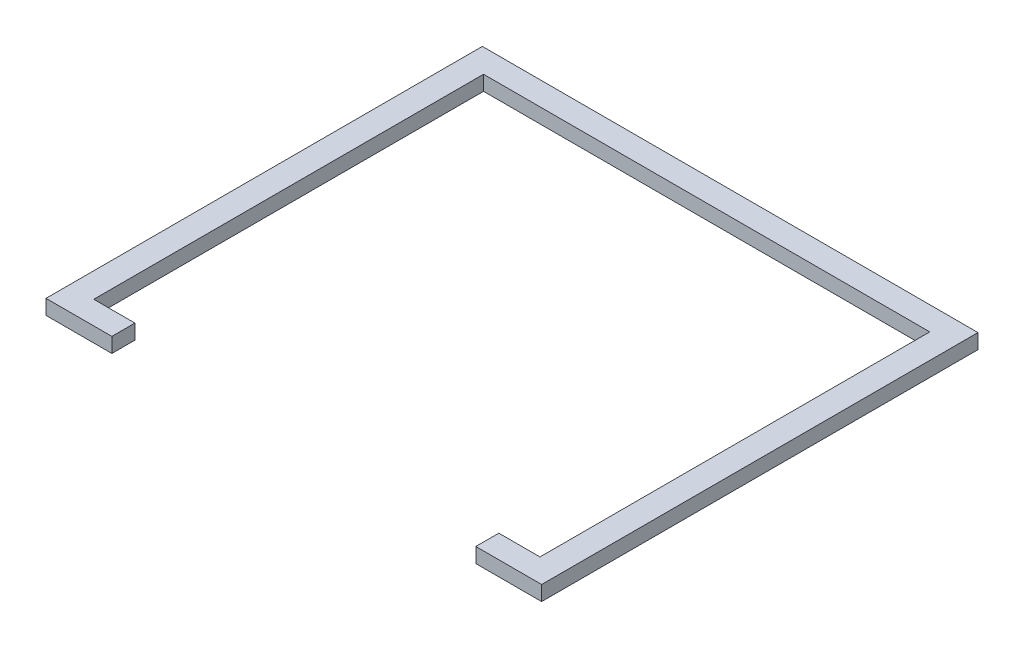
SolidWorks part; units mm, degrees
ref_plane "前视基准面" through (0, 0, 0) normal (0, 0, 1) x (1, 0, 0)
ref_plane "上视基准面" through (0, 0, 0) normal (0, 1, 0) x (1, 0, 0)
ref_plane "右视基准面" through (0, 0, 0) normal (1, 0, 0) x (0, 0, -1)
sketch "草图1" plane through (0, 0, 0) normal (0, 1, 0) x (1, 0, 0)
  line B0 (-1401.586, -1568.3025) -> (-1801.586, -1568.3025)
  line B1 (-1801.586, -1568.3025) -> (-1801.586, 1081.6975)
  line B2 (-1801.586, 1081.6975) -> (1208.3796, 1081.6975)
  line B3 (1208.3796, 1081.6975) -> (1208.3796, -1568.3025)
  line B4 (1208.3796, -1568.3025) -> (808.3796, -1568.3025)
  line B5 (-1401.586, -1568.3025) -> (-1401.586, -1428.3025)
  line B6 (-1401.586, -1428.3025) -> (-1651.586, -1428.3025)
  line B7 (-1651.586, -1428.3025) -> (-1651.586, 938.7842)
  line B8 (-1651.586, 938.7842) -> (1058.3796, 938.7842)
  line B9 (1058.3796, 938.7842) -> (1058.3796, -1428.3025)
  line B10 (1058.3796, -1428.3025) -> (808.3796, -1428.3025)
  line B11 (808.3796, -1428.3025) -> (808.3796, -1568.3025)
sketch_block_instance "块-Tingfs-1"
sketch_block "块-Tingfs"
extrude "凸台-拉伸1" add sketch "草图1" along normal blind 90
